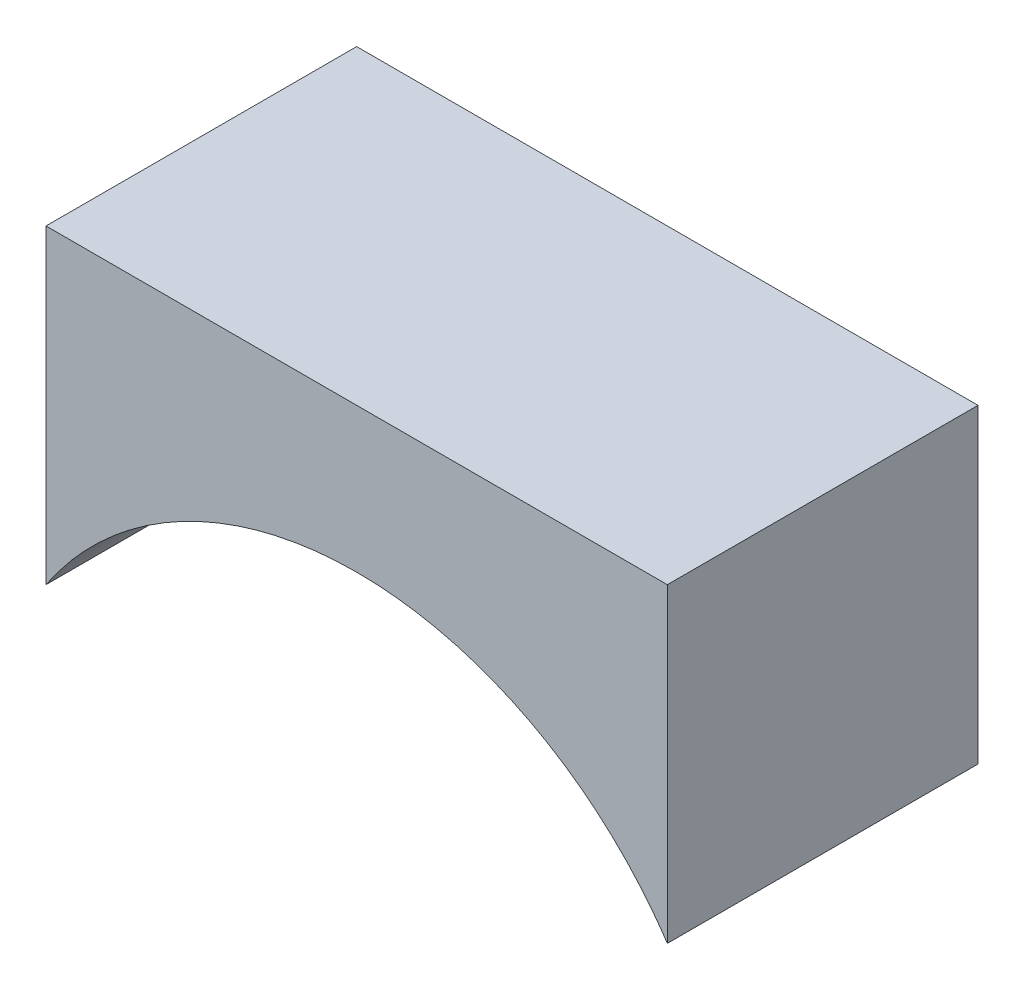
SolidWorks part; units mm, degrees
material "Silicon"
ref_plane "Front Plane" through (0, 0, 0) normal (0, 0, 1) x (1, 0, 0)
ref_plane "Top Plane" through (0, 0, 0) normal (0, 1, 0) x (1, 0, 0)
ref_plane "Right Plane" through (0, 0, 0) normal (1, 0, 0) x (0, 0, -1)
sketch "Sketch1" plane through (0, 0, 0) normal (0, 0, 1) x (1, 0, 0)
  line L2 (1400.1305, -323.2791) -> (1400.1305, -173.2791)
  line L3 (1400.1305, -173.2791) -> (1700.1305, -173.2791)
  line L4 (1700.1305, -323.2791) -> (1700.1305, -173.2791)
  spline S0 degree 3 poles (1489.7865, -594.5549) (1524.3401, -603.0384) (1559.8848, -604.6178) (1595.0546, -599.2324) (1628.4981, -587.0893) (1658.9299, -568.6549) (1685.1806, -544.6378) (1706.2414, -515.961) (1721.303, -483.7263) (1729.7865, -449.1728) (1731.3659, -413.628) (1725.9806, -378.4582) (1713.8374, -345.0147) (1695.403, -314.5829) (1671.386, -288.3322) (1642.7091, -267.2714) (1610.4745, -252.2098) (1575.9209, -243.7263) (1540.3762, -242.1469) (1505.2063, -247.5322) (1471.7629, -259.6754) (1441.3311, -278.1098) (1415.0803, -302.1268) (1394.0195, -330.8037) (1378.9579, -363.0383) (1370.4744, -397.5919) (1368.895, -433.1366) (1374.2804, -468.3065) (1386.4236, -501.7499) (1404.8579, -532.1818) (1428.875, -558.4325) (1457.5518, -579.4933) (1489.7865, -594.5549) (1524.3401, -603.0384) (1559.8848, -604.6178) knots -0.589049 -0.392699 -0.19635 0 0.19635 0.392699 0.589049 0.785398 0.981748 1.178097 1.374447 1.570796 1.767146 1.963495 2.159845 2.356194 2.552544 2.748894 2.945243 3.141593 3.337942 3.534292 3.730641 3.926991 4.12334 4.31969 4.516039 4.712389 4.908739 5.105088 5.301438 5.497787 5.694137 5.890486 6.086836 6.283185 6.479535 6.675884 6.872234 only from (1524.5052, -601.8877) to (1524.5052, -601.8877) construction
  spline S1 degree 3 poles (1700.1305, -323.2791) (1698.3174, -320.5621) (1689.6129, -308.2543) (1671.386, -288.3322) (1642.7091, -267.2714) (1610.4745, -252.2098) (1575.9209, -243.7263) (1540.3762, -242.1469) (1505.2063, -247.5322) (1471.7629, -259.6754) (1441.3311, -278.1098) (1417.4511, -299.9578) (1404.9075, -316.1219) (1400.1305, -323.2791) knots 2.301855 2.301855 2.301855 2.301855 2.356194 2.552544 2.748894 2.945243 3.141593 3.337942 3.534292 3.730641 3.926991 4.12334 4.26649 4.26649 4.26649 4.26649
  dimension "D1" = 150
  dimension "D2" = 300
extrude "Boss-Extrude1" add sketch "Sketch1" against normal blind 150
